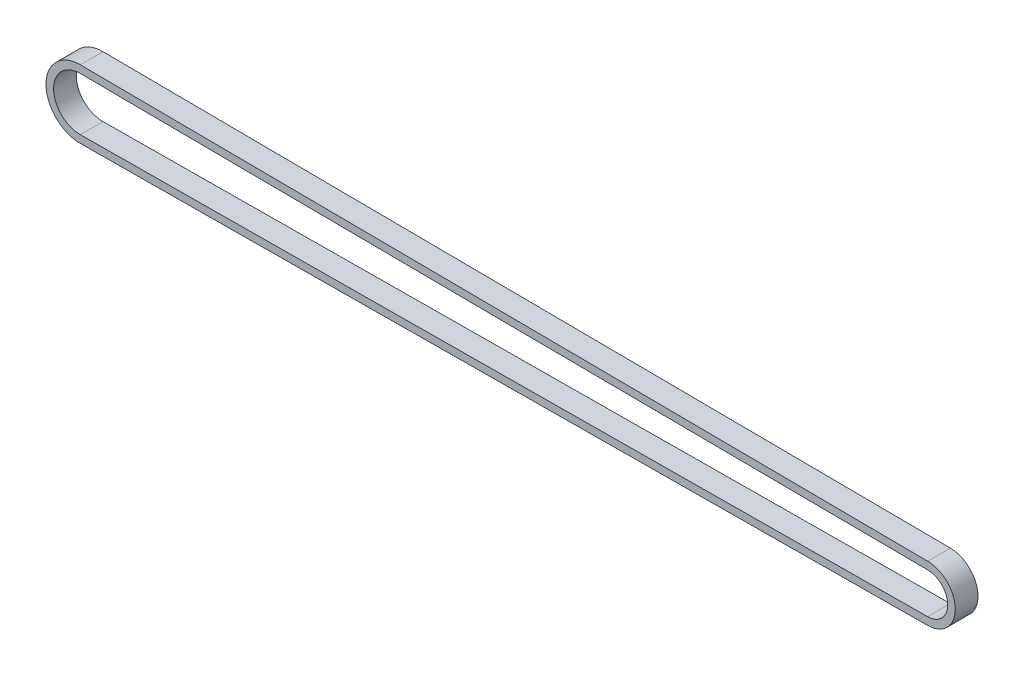
SolidWorks part; units mm, degrees
ref_plane "Front Plane" through (0, 0, 0) normal (0, 0, 1) x (1, 0, 0)
ref_plane "Top Plane" through (0, 0, 0) normal (0, 1, 0) x (1, 0, 0)
ref_plane "Right Plane" through (0, 0, 0) normal (1, 0, 0) x (0, 0, -1)
sketch "Sketch1" plane through (0, 0, 0) normal (0, 0, 1) x (1, 0, 0)
  line L0 (112.8626, -5.3534) -> (-111.1253, -6.9998)
  line L1 (-111.1253, 6.9998) -> (112.8626, 5.3534)
  line L2 (112.8773, -7.3534) -> (-111.1106, -8.9998)
  line L3 (-111.1106, 8.9998) -> (112.8773, 7.3534)
  arc A0 (112.8626, 5.3534) -> (112.8626, -5.3534) centre (112.8232, 0) cw
  arc A1 (-111.1253, -6.9998) -> (-111.1253, 6.9998) centre (-111.1768, 0) cw
  arc A2 (112.8773, 7.3534) -> (112.8773, -7.3534) centre (112.8232, 0) cw
  arc A3 (-111.1106, -8.9998) -> (-111.1106, 8.9998) centre (-111.1768, 0) cw
  dimension "D1" = 2
extrude "Boss-Extrude1" add sketch "Sketch1" along normal blind 6
